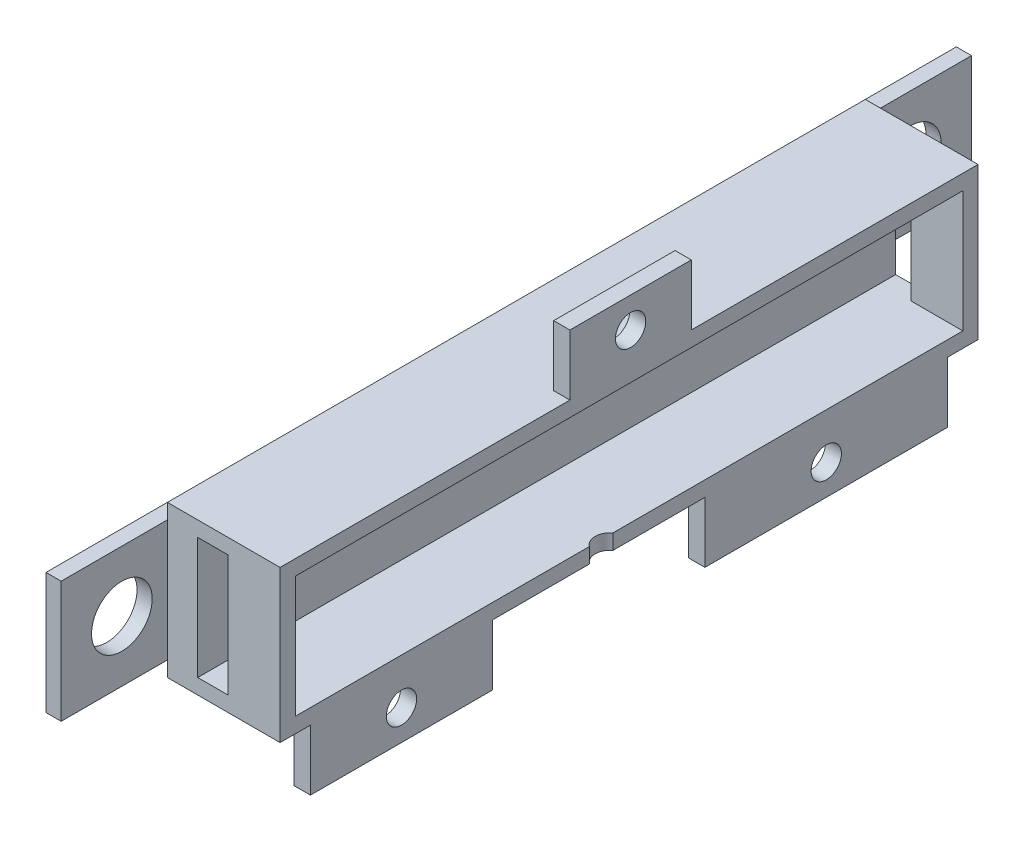
SolidWorks part; units mm, degrees
ref_plane "Front" through (0, 0, 0) normal (0, 0, 1) x (1, 0, 0)
ref_plane "Top" through (0, 0, 0) normal (0, 1, 0) x (1, 0, 0)
ref_plane "Right" through (0, 0, 0) normal (1, 0, 0) x (0, 0, -1)
sketch "Sketch1" plane through (0, 0, 0) normal (1, 0, 0) x (0, 0, -1)
  line L0 (-145.5208, 2.1167) -> (-145.5208, 14.8167)
  line L1 (-132.8208, 14.8167) -> (32.2792, 14.8167)
  line L2 (-132.8208, 14.8167) -> (-132.8208, -10.5833)
  line L3 (-132.8208, -10.5833) -> (32.2792, -10.5833)
  line L4 (32.2792, 14.8167) -> (32.2792, -10.5833)
  line L5 (-145.5208, 14.8167) -> (-132.8208, 14.8167)
  line L6 (-145.5208, 2.1167) -> (-145.5208, -10.5833)
  line L7 (-145.5208, -10.5833) -> (-132.8208, -10.5833)
  line L8 (44.9792, 2.1167) -> (44.9792, -10.5833)
  line L9 (44.9792, -10.5833) -> (32.2792, -10.5833)
  line L10 (32.2792, 14.8167) -> (44.9792, 14.8167)
  line L11 (44.9792, 14.8167) -> (44.9792, 2.1167)
  line L13 (-145.5208, 14.8167) -> (44.9792, 14.8167)
  line L14 (-145.5208, 14.8167) -> (-145.5208, -10.5833)
  line L15 (-145.5208, -10.5833) -> (44.9792, -10.5833)
  line L16 (44.9792, 14.8167) -> (44.9792, -10.5833)
  circle A2 centre (-132.8208, 2.1167) radius 6.35
  circle A3 centre (32.2792, 2.1167) radius 6.35
  dimension "D3" = 12.7
  dimension "D4" = 165.1
  dimension "D2" = 25.4
extrude "Boss-Extrude1" add sketch "Sketch1" along normal blind 3.175 contours A2 L2 L5 L0 L6 L7 | A3 L4 L1 L2 A2 L3 | A3 L4 L9 L8 L11 L10
sketch "Sketch2" plane through (3.175, 0, 0) normal (1, 0, 0) x (0, 0, -1)
  line L0 (-145.5208, -10.5833) -> (44.9792, -10.5833) construction
  line L1 (-145.5208, 14.8167) -> (45.002, 14.8167)
  line L2 (-145.5208, 14.8167) -> (-145.5208, 17.9917)
  line L3 (-145.5208, 17.9917) -> (45.002, 17.9917)
  line L4 (45.002, 14.8167) -> (45.002, 17.9917)
  line L5 (-123.2958, 14.8167) -> (22.7542, 14.8167)
  line L6 (-123.2958, 14.8167) -> (-123.2958, -10.5833)
  line L7 (-123.2958, -10.5833) -> (22.7542, -10.5833)
  line L8 (22.7542, 14.8167) -> (22.7542, -10.5833)
  line L9 (44.9792, 14.8167) -> (44.9792, -10.5833) construction
  line L10 (-145.5208, -10.5833) -> (45.002, -10.5833)
  line L11 (-145.5208, -10.5833) -> (-145.5208, -13.7583)
  line L12 (-145.5208, -13.7583) -> (45.002, -13.7583)
  line L13 (45.002, -10.5833) -> (45.002, -13.7583)
  line L14 (-145.5208, -10.5833) -> (-145.5208, 14.8167) construction
  line L15 (-123.2958, -10.5833) -> (-123.2958, -13.7583)
  line L16 (-123.2958, 14.8167) -> (-123.2958, 17.9917)
  line L17 (22.7542, -10.5833) -> (22.7542, -13.7583)
  line L18 (22.7542, 14.8167) -> (22.7542, 17.9917)
  line M12 (-145.5208, -10.5833) -> (44.9792, -10.5833)
  dimension "D1" = 3.175
  dimension "D2" = 3.175
  dimension "D3" = 22.225
  dimension "D4" = 22.225
extrude "Boss-Extrude2" add sketch "Sketch2" along normal blind 47.625 separate body contours L17 L15 L12 M12 | L1 L18 L3 L16
sketch "Sketch3" plane through (3.175, 0, 0) normal (1, 0, 0) x (0, 0, -1)
  line L1 (-123.2958, 14.8167) -> (22.7542, 14.8167)
  line L2 (-123.2958, 14.8167) -> (-123.2958, -10.5833)
  line L3 (-123.2958, -10.5833) -> (22.7542, -10.5833)
  line L4 (22.7542, 14.8167) -> (22.7542, -10.5833)
extrude "Boss-Extrude4" add sketch "Sketch3" along normal blind 6.35
sketch "Sketch4" plane through (9.525, 0, 0) normal (1, 0, 0) x (0, 0, -1)
  line L6 (-123.2958, -10.5833) -> (22.7542, -10.5833) construction
  line L7 (-123.2958, 14.8167) -> (-120.1208, 14.8167)
  line L8 (-123.2958, 14.8167) -> (-123.2958, -10.5833)
  line L9 (-123.2958, -10.5833) -> (-120.1208, -10.5833)
  line L10 (-120.1208, 14.8167) -> (-120.1208, -10.5833)
  line L12 (22.7542, 14.8167) -> (19.5792, 14.8167)
  line L13 (22.7542, 14.8167) -> (22.7542, -10.5833)
  line L14 (22.7542, -10.5833) -> (19.5792, -10.5833)
  line L15 (19.5792, 14.8167) -> (19.5792, -10.5833)
  dimension "D1" = 3.175
  dimension "D2" = 3.175
extrude "Boss-Extrude5" add sketch "Sketch4" along normal blind 41.275
sketch "Sketch5" plane through (0, 0, 123.2958) normal (0, 0, 1) x (1, 0, 0)
  line L0 (50.8, 17.9917) -> (3.175, 17.9917) construction
  line L1 (9.525, 17.9917) -> (15.875, 17.9917)
  line L2 (9.525, 17.9917) -> (9.525, -13.7583)
  line L3 (9.525, -13.7583) -> (15.875, -13.7583)
  line L4 (15.875, 17.9917) -> (15.875, -13.7583)
  line L5 (50.8, -13.7583) -> (3.175, -13.7583) construction
  line L6 (3.175, 14.8167) -> (3.175, -10.5833) construction
  line L7 (9.525, 14.8167) -> (15.875, 14.8167)
  line L8 (9.525, -10.5833) -> (15.875, -10.5833)
  dimension "D1" = 6.35
  dimension "D2" = 6.35
  dimension "D3" = 3.175
  dimension "D4" = 3.175
extrude "Cut-Extrude1" cut sketch "Sketch5" against normal blind 165.45 contours L2 L8 L4 L7
sketch "Sketch7" plane through (50.8, 0, 0) normal (1, 0, 0) x (0, 0, -1)
  line L1 (-123.2958, 17.9917) -> (22.7542, 17.9917)
  line L2 (-123.2958, 17.9917) -> (-123.2958, -13.7583)
  line L3 (-123.2958, -13.7583) -> (22.7542, -13.7583)
  line L4 (22.7542, 17.9917) -> (22.7542, -13.7583)
extrude "Boss-Extrude7" add sketch "Sketch7" along normal blind 3.175
fillet "Fillet1" radius 10 4 edges at (53.975, 17.9917, 50.2708) (53.975, 2.1167, -22.7542) (53.975, -13.7583, 50.2708) (53.975, 2.1167, 123.2958)
sketch "Sketch8" plane through (0, -13.7583, 0) normal (0, -1, 0) x (1, 0, 0)
  line L0 (43.975, 123.2958) -> (3.175, 123.2958) construction
  line L3 (3.175, 123.2958) -> (3.175, -22.7542) construction
  circle A0 centre (28.575, 56.1208) radius 3.05
  dimension "D3" = 6.1
  dimension "D1" = 67.175
  dimension "D2" = 25.4
extrude "Cut-Extrude2" cut sketch "Sketch8" against normal blind 3.175
sketch "Sketch9" plane through (0, -13.7583, 0) normal (0, -1, 0) x (1, 0, 0)
  line L0 (43.975, 123.2958) -> (3.175, 123.2958) construction
  line L1 (29.7167, 116.9458) -> (23.3667, 116.9458)
  line L2 (29.7167, 116.9458) -> (29.7167, 78.8458)
  line L3 (29.7167, 78.8458) -> (23.3667, 78.8458)
  line L4 (23.3667, 116.9458) -> (23.3667, 78.8458)
  line L5 (29.7167, 34.3958) -> (23.3667, 34.3958)
  line L6 (29.7167, 34.3958) -> (29.7167, -16.4042)
  line L7 (29.7167, -16.4042) -> (23.3667, -16.4042)
  line L8 (23.3667, 34.3958) -> (23.3667, -16.4042)
  line L9 (43.975, -22.7542) -> (3.175, -22.7542) construction
  dimension "D1" = 6.35
  dimension "D2" = 50.8
  dimension "D3" = 6.35
  dimension "D4" = 38.1
  dimension "D5" = 6.35
  dimension "D6" = 6.35
  dimension "D7" = 20.1917
extrude "Boss-Extrude8" add sketch "Sketch9" along normal blind 12.7
sketch "Sketch10" plane through (29.7167, 0, 0) normal (1, 0, 0) x (0, 0, -1)
  line L0 (-34.3958, -26.4583) -> (-34.3958, -13.7583) construction
  line L1 (16.4042, -26.4583) -> (-34.3958, -26.4583) construction
  line L2 (-78.8458, -26.4583) -> (-116.9458, -26.4583) construction
  line L3 (-78.8458, -26.4583) -> (-78.8458, -13.7583) construction
  circle A0 centre (-97.8958, -20.1083) radius 3.175
  circle A1 centre (-8.9958, -20.1083) radius 3.175
  dimension "D1" = 6.35
  dimension "D2" = 6.35
  dimension "D3" = 25.4
  dimension "D4" = 6.35
  dimension "D5" = 6.35
  dimension "D6" = 19.05
extrude "Cut-Extrude3" cut sketch "Sketch10" against normal blind 12.7
sketch "Sketch11" plane through (0, 17.9917, 0) normal (0, 1, 0) x (1, 0, 0)
  line L0 (43.975, 22.7542) -> (3.175, 22.7542) construction
  line L1 (29.715, -37.2458) -> (23.365, -37.2458)
  line L2 (29.715, -37.2458) -> (29.715, -62.6458)
  line L3 (29.715, -62.6458) -> (23.365, -62.6458)
  line L4 (23.365, -37.2458) -> (23.365, -62.6458)
  dimension "D1" = 60
  dimension "D2" = 25.4
  dimension "D3" = 6.35
  dimension "D4" = 20.19
extrude "Boss-Extrude9" add sketch "Sketch11" along normal blind 12.7
sketch "Sketch12" plane through (29.715, 0, 0) normal (1, 0, 0) x (0, 0, -1)
  line L0 (-37.2458, 30.6917) -> (-37.2458, 17.9917) construction
  line L3 (-62.6458, 30.6917) -> (-37.2458, 30.6917) construction
  circle A0 centre (-49.9458, 24.3417) radius 3.175
  dimension "D3" = 6.35
  dimension "D1" = 12.7
  dimension "D2" = 6.35
extrude "Cut-Extrude4" cut sketch "Sketch12" against normal blind 12.7
sketch "Sketch13" plane through (0, -13.7583, 0) normal (0, -1, 0) x (1, 0, 0)
  line L0 (43.975, 123.2958) -> (3.175, 123.2958) construction
  line L1 (26.7612, 123.2958) -> (55.5015, 123.2958)
  line L2 (26.7612, 123.2958) -> (26.7612, -22.8245)
  line L3 (26.7612, -22.8245) -> (55.5015, -22.8245)
  line L4 (55.5015, 123.2958) -> (55.5015, -22.8245)
extrude "Cut-Extrude5" cut sketch "Sketch13" against normal blind 50.8 and the other way blind 50.8
